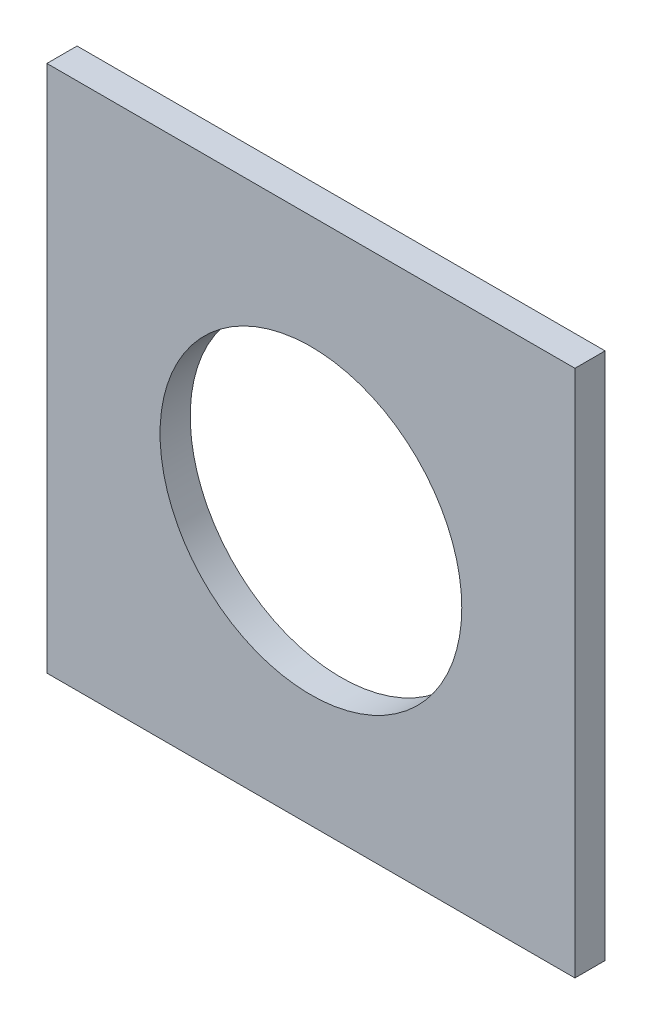
SolidWorks part; units mm, degrees
ref_plane "Alzado" through (0, 0, 0) normal (0, 0, 1) x (1, 0, 0)
ref_plane "Planta" through (0, 0, 0) normal (0, 1, 0) x (1, 0, 0)
ref_plane "Vista lateral" through (0, 0, 0) normal (1, 0, 0) x (0, 0, -1)
sketch "Croquis1" plane through (0, 0, 0) normal (0, 0, 1) x (1, 0, 0)
  line L1 (-350, 350) -> (350, 350)
  line L2 (-350, 350) -> (-350, -350)
  line L3 (-350, -350) -> (350, -350)
  line L4 (350, 350) -> (350, -350)
  line L5 (-350, 350) -> (350, -350) construction
  line L6 (-350, -350) -> (350, 350) construction
  point P0 (0, 0)
  dimension "D1" = 700
  dimension "D2" = 700
extrude "Saliente-Extruir1" add sketch "Croquis1" along normal blind 40
sketch "Croquis2" plane through (0, 0, 40) normal (0, 0, 1) x (1, 0, 0)
  circle A0 centre (0, 0) radius 200
  dimension "D1" = 400
extrude "Cortar-Extruir1" cut sketch "Croquis2" against normal through all
